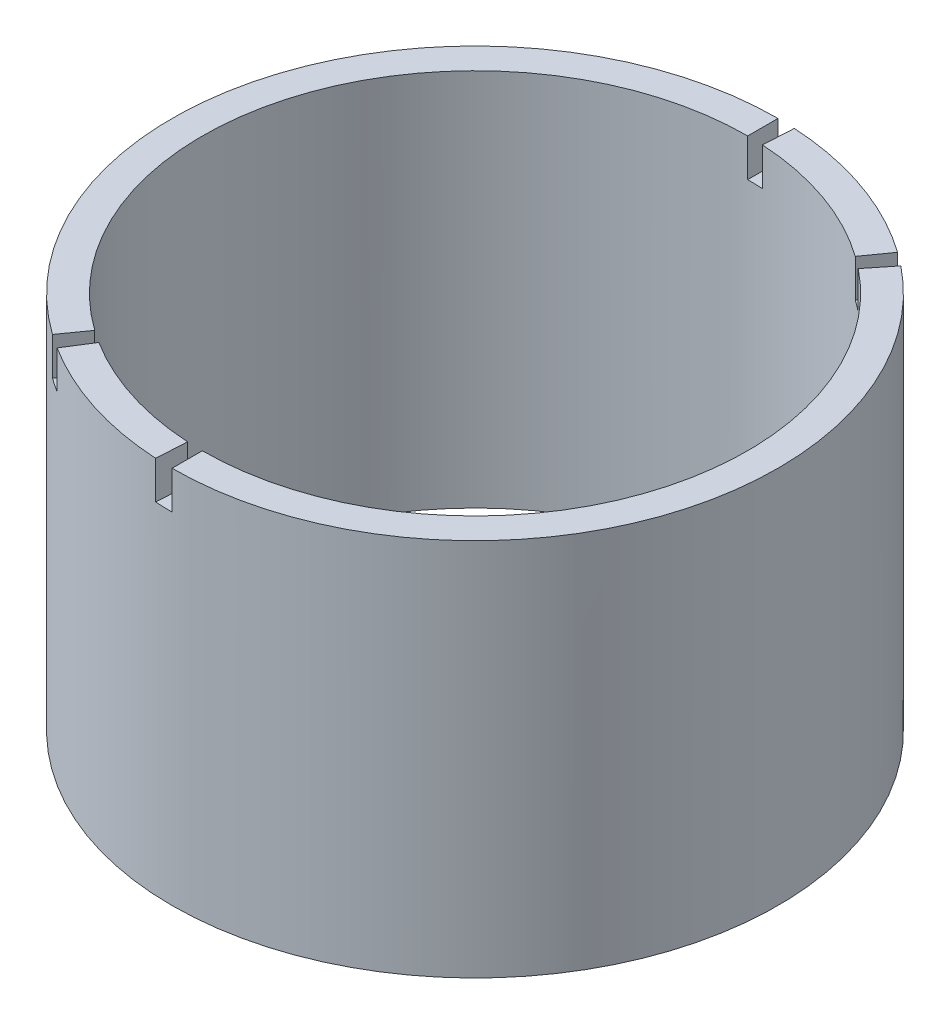
SolidWorks part; units mm, degrees
ref_plane "Plan de face" through (0, 0, 0) normal (0, 0, 1) x (1, 0, 0)
ref_plane "Plan de dessus" through (0, 0, 0) normal (0, 1, 0) x (1, 0, 0)
ref_plane "Plan de droite" through (0, 0, 0) normal (1, 0, 0) x (0, 0, -1)
sketch "Esquisse1" plane through (0, 0, 0) normal (0, 1, 0) x (1, 0, 0)
  circle A0 centre (0, 0) radius 40
  circle A1 centre (0, 0) radius 36
  dimension "D1" = 80
  dimension "D2" = 4
extrude "Extrusion1" add sketch "Esquisse1" along normal blind 50
sketch "Esquisse2" plane through (0, 50, 0) normal (0, 1, 0) x (1, 0, 0)
  line L0 (0, 0) -> (0, 40) construction
  line L1 (0, 0) -> (0, -40) construction
  line L2 (0, -40) -> (0, -36)
  line L3 (0, 40) -> (0, 36)
  line L4 (0, 0) -> (2.2222, 39.9382) construction
  line L5 (0, 0) -> (-2.2222, -39.9382) construction
  line L6 (-2.2222, -39.9382) -> (-2, -35.9444)
  line L7 (2.2222, 39.9382) -> (2, 35.9444)
  line L8 (0, 0) -> (23.194, 32.5889) construction
  line L9 (23.194, 32.5889) -> (20.8746, 29.33)
  line L10 (0, 0) -> (24.968, 31.2506) construction
  line L11 (24.968, 31.2506) -> (22.4712, 28.1255)
  line L12 (0, 0) -> (-21.3484, -33.8267) construction
  line L13 (-21.3484, -33.8267) -> (-19.2136, -30.444)
  line L14 (0, 0) -> (-23.194, -32.5889) construction
  line L15 (-23.194, -32.5889) -> (-20.8746, -29.33)
  circle A0 centre (0, 0) radius 40 construction
  circle A1 centre (0, 0) radius 36 construction
  arc A2 (0, 40) -> (2.2222, 39.9382) centre (0, 0) cw
  arc A3 (0, 36) -> (2, 35.9444) centre (0, 0) cw
  arc A4 (-2, -35.9444) -> (0, -36) centre (0, 0) ccw
  arc A5 (-2.2222, -39.9382) -> (0, -40) centre (0, 0) ccw
  arc A6 (23.194, 32.5889) -> (24.968, 31.2506) centre (0, 0) cw
  arc A7 (20.8746, 29.33) -> (22.4712, 28.1255) centre (0, 0) cw
  circle A8 centre (0, 0) radius 40 construction
  circle A9 centre (0, 0) radius 36 construction
  arc A10 (-21.3484, -33.8267) -> (-23.194, -32.5889) centre (0, 0) cw
  arc A11 (-19.2136, -30.444) -> (-20.8746, -29.33) centre (0, 0) cw
  circle A12 centre (0, 0) radius 40 construction
  circle A13 centre (0, 0) radius 36 construction
  dimension "D1" = 2
  dimension "D2" = 2
  dimension "D3" = 20
  dimension "D4" = 2
extrude "Extrusion2" cut sketch "Esquisse2" against normal blind 5
